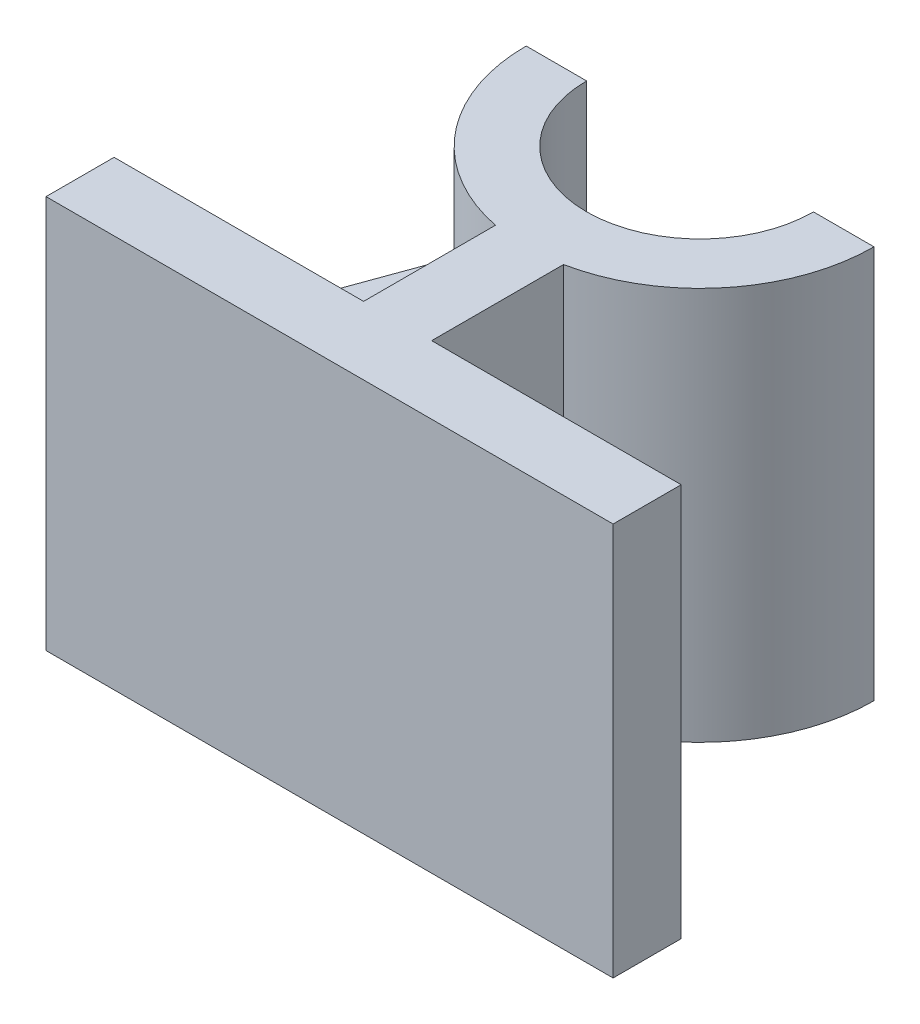
SolidWorks part; units mm, degrees
ref_plane "Front Plane" through (0, 0, 0) normal (0, 0, 1) x (1, 0, 0)
ref_plane "Top Plane" through (0, 0, 0) normal (0, 1, 0) x (1, 0, 0)
ref_plane "Right Plane" through (0, 0, 0) normal (1, 0, 0) x (0, 0, -1)
sketch "Sketch8" plane through (0, 0, 0) normal (0, 1, 0) x (1, 0, 0)
  line L0 (37.5, 4.5) -> (4.5, 4.5) construction
  line L1 (-37.5, 4.5) -> (37.5, 4.5)
  line L2 (-37.5, 4.5) -> (-37.5, -4.5)
  line L3 (-37.5, -4.5) -> (37.5, -4.5)
  line L4 (37.5, 4.5) -> (37.5, -4.5)
  line L5 (-37.5, 4.5) -> (37.5, -4.5) construction
  line L6 (-37.5, -4.5) -> (37.5, 4.5) construction
  line L7 (0, 4.5) -> (0, 29.5) construction
  line L8 (4.5, 4.5) -> (-4.5, 4.5)
  line L9 (4.5, 4.5) -> (4.5, 21.5)
  line L11 (-4.5, 4.5) -> (-4.5, 21.5)
  line L12 (-4.5, 21.5) -> (-4.5, 21.9445)
  line L13 (4.5, 21.5) -> (4.5, 21.9445)
  line L14 (-23, 44.5) -> (-15, 44.5)
  line L15 (15, 44.5) -> (23, 44.5)
  arc A0 (4.5, 21.9445) -> (23, 44.5) centre (0, 44.5) ccw
  arc A1 (-15, 44.5) -> (15, 44.5) centre (0, 44.5) ccw
  arc A2 (-23, 44.5) -> (-4.5, 21.9445) centre (0, 44.5) ccw
  point P0 (0, 0)
  dimension "D1" = 75
  dimension "D2" = 9
  dimension "D3" = 17
  dimension "D4" = 9
extrude "Boss-Extrude5" add sketch "Sketch8" against normal blind 52 contours L14 A2 L12 L11 L1 L9 L13 A0 L15 A1 | L4 L1 L2 L3
ref_plane "Plane2" through (0, -30, 0) normal (0, -1, 0) x (-1, 0, 0)
sketch "Sketch9" plane through (0, -30, 0) normal (0, -1, 0) x (-1, 0, 0)
  line L0 (23, 44.5) -> (37.5, 4.5)
  line L1 (37.5, 4.5) -> (4.5, 4.5)
  line L2 (4.5, 4.5) -> (4.5, 21.9445)
  arc A0 (4.5, 21.9445) -> (23, 44.5) centre (0, 44.5) ccw
extrude "Boss-Extrude6" add sketch "Sketch9" against normal blind 8
